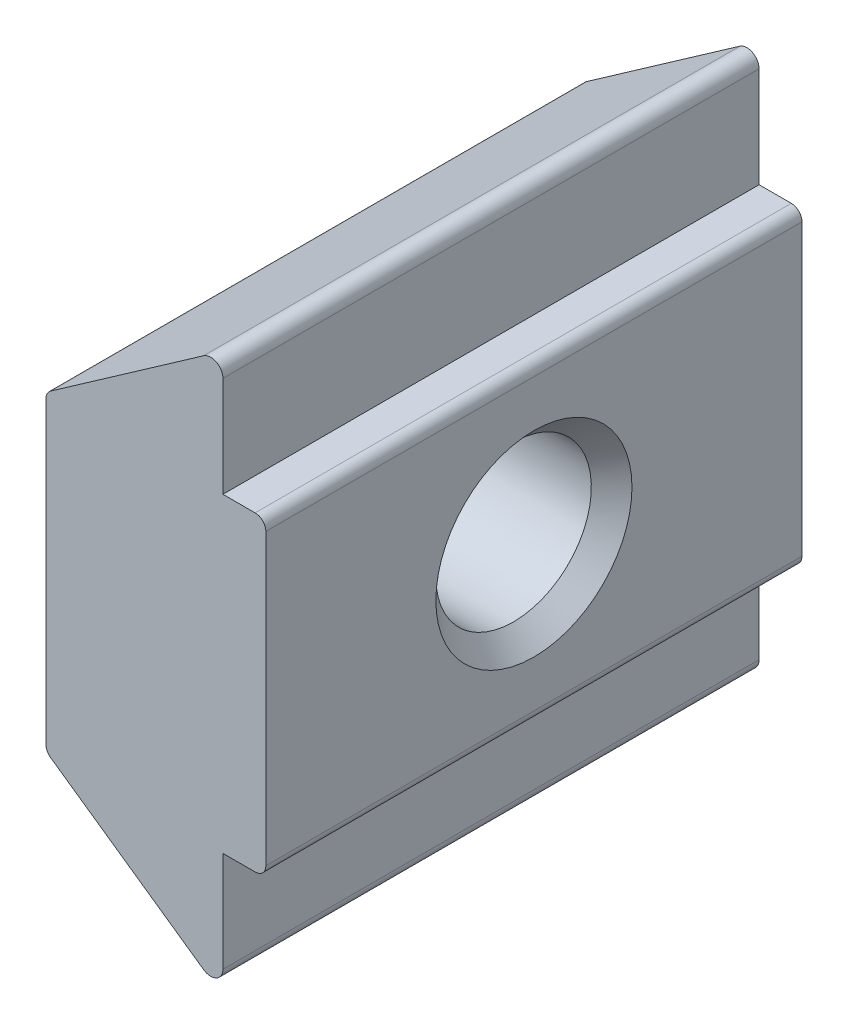
SolidWorks part; units mm, degrees
material "Stainless Steel (ferritic)"
ref_plane "Front Plane" through (0, 0, 0) normal (0, 0, 1) x (1, 0, 0)
ref_plane "Top Plane" through (0, 0, 0) normal (0, 1, 0) x (1, 0, 0)
ref_plane "Right Plane" through (0, 0, 0) normal (1, 0, 0) x (0, 0, -1)
ref_plane "Plane1" through (0, 0, 5) normal (0, 0, 1) x (1, 0, 0)
sketch "Sketch1" plane through (0, 0, 5) normal (0, 0, 1) x (1, 0, 0)
  line L0 (-0.8, -4.7719) -> (-0.8, 4.7719)
  line L1 (-1.1589, 4.9588) -> (-4.1, 2.9)
  line L2 (-4.1, 2.9) -> (-4.1, -2.9)
  line L3 (-4.1, -2.9) -> (-1.1589, -4.9588)
  arc A0 (-1.1589, -4.9588) -> (-0.8, -4.7719) centre (-1.0281, -4.7719) ccw
  arc A1 (-0.8, 4.7719) -> (-1.1589, 4.9588) centre (-1.0281, 4.7719) ccw
extrude "Boss-Extrude1" add sketch "Sketch1" against normal blind 10
sketch "Sketch2" plane through (-0.8, 0, 0) normal (1, 0, 0) x (0, 0, -1)
  line L0 (5, 2.9) -> (5, -2.9)
  line L1 (5, -2.9) -> (-5, -2.9)
  line L2 (-5, -2.9) -> (-5, 2.9)
  line L3 (-5, 2.9) -> (5, 2.9)
extrude "Boss-Extrude2" add sketch "Sketch2" along normal blind 0.8
hole_wizard "Tap Drill for M3.5x0.6 Tap1" positions "Sketch4" profile "Sketch3" hole size "M3.5x0.6" standard "ANSI Metric" end condition through all
sketch "Sketch4" plane through (0, 0, 0) normal (1, 0, 0) x (0, 0, -1)
  point P0 (0, 0)
sketch "Sketch3" plane through (0, 0, 0) normal (0, 1, 0) x (0, 0, -1)
  line L0 (0, 0) -> (0, 4.1)
  line L1 (0, 4.1) -> (1.45, 4.1)
  line L2 (1.45, 4.1) -> (1.45, 0)
  line L5 (1.45, 0) -> (0, 0)
  line L11 (0, -6.35) -> (0, 107.95) construction
  dimension "Thru Hole Dia." = 2.9
  dimension "Thru Hole Depth" = 4.1
chamfer "Chamfer1" distance 0.379 angle 45 2 edges at (-4.1, 0, -1.45) (0, 0, -1.45)
fillet "Fillet1" radius 0.2 4 edges at (-4.1, -2.9, 0) (-4.1, 2.9, 0) (0, 2.9, 0) (0, -2.9, 0)
